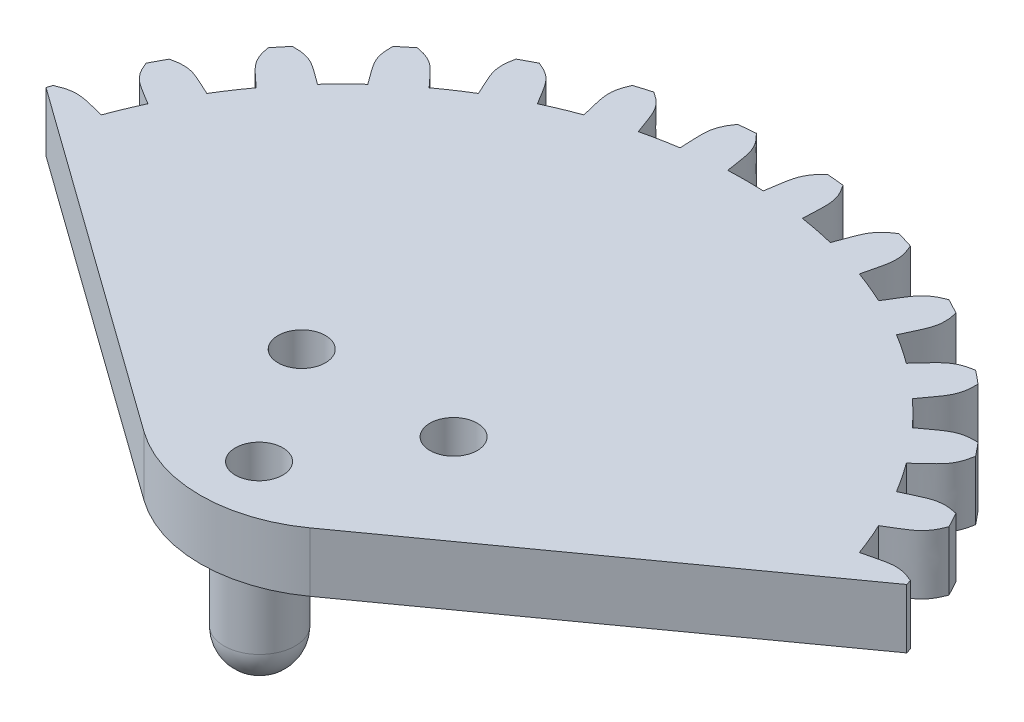
SolidWorks part; units mm, degrees
ref_plane "Front Plane" through (0, 0, 0) normal (0, 0, 1) x (1, 0, 0)
ref_plane "Top Plane" through (0, 0, 0) normal (0, 1, 0) x (1, 0, 0)
ref_plane "Right Plane" through (0, 0, 0) normal (1, 0, 0) x (0, 0, -1)
sketch "Sketch1" plane through (0, 0, 0) normal (0, 1, 0) x (1, 0, 0)
  line L2 (18.1445, 5.6371) -> (3.4985, -4.8745)
  line L3 (-18.1445, 5.6371) -> (-3.4985, -4.8745)
  arc A0 (18.1445, 5.6371) -> (-18.1445, 5.6371) centre (0, 0) ccw
  arc A2 (-3.4985, -4.8745) -> (3.4985, -4.8745) centre (0, 0) ccw
  dimension "D1" = 19
  dimension "D2" = 108.665
  dimension "D4" = 12
extrude "Boss-Extrude1" add sketch "Sketch1" along normal blind 2.5 contours L3 A2 L2 A0
sketch "Sketch2" plane through (0, 0, 0) normal (0, -1, 0) x (1, 0, 0)
  circle A0 centre (0, 0) radius 0.25
  dimension "D1" = 0.5
extrude "Boss-Extrude2" add sketch "Sketch2" along normal blind 0.2
sketch "Sketch4" plane through (0, 2.5, 0) normal (0, 1, 0) x (1, 0, 0)
  line L0 (0, 19) -> (0, 0) construction
  circle A0 centre (0, 0) radius 17
  arc A1 (18.1445, 5.6371) -> (-18.1445, 5.6371) centre (0, 0) ccw construction
  spline S0 degree 3 poles (-1.5, 18.9407) (-0.8621, 18.3427) (-0.9212, 17.9638) (-0.75, 16.9834) knots 0 0 0 0 1 1 1 1
  spline S1 degree 3 poles (1.5, 18.9407) (0.8621, 18.3427) (0.9212, 17.9638) (0.75, 16.9834) knots 0 0 0 0 1 1 1 1
  dimension "D1" = 2
  dimension "D3" = 1.5
  dimension "D4" = 0.75
extrude "Cut-Extrude2" cut sketch "Sketch4" against normal blind 3.5
pattern_circular "CirPattern1" count 32 over 360 about axis through (0, 0, 0) along (0, 1, 0) of "Cut-Extrude2"
sketch "Sketch6" plane through (0, 2.5, 0) normal (0, 1, 0) x (1, 0, 0)
  circle A0 centre (0, 0) radius 3.525 construction
  circle A1 centre (-3.2016, 1.475) radius 1
  circle A2 centre (3.2016, 1.475) radius 1
  circle A3 centre (0, -3.525) radius 1
  dimension "D1" = 7.05
  dimension "D4" = 2
  dimension "D5" = 2
  dimension "D6" = 2
  dimension "D2" = 5
  dimension "D3" = 5
extrude "Cut-Extrude3" cut sketch "Sketch6" against normal blind 2
sketch "Sketch7" plane through (0, 0, 0) normal (0, -1, 0) x (1, 0, 0)
  circle A0 centre (0, 3.5) radius 1.5
  dimension "D1" = 3
  dimension "D2" = 3.5
extrude "Boss-Extrude3" add sketch "Sketch7" along normal blind 5
fillet "Fillet1" radius 1.5 1 edges at (0, -5, 2)
